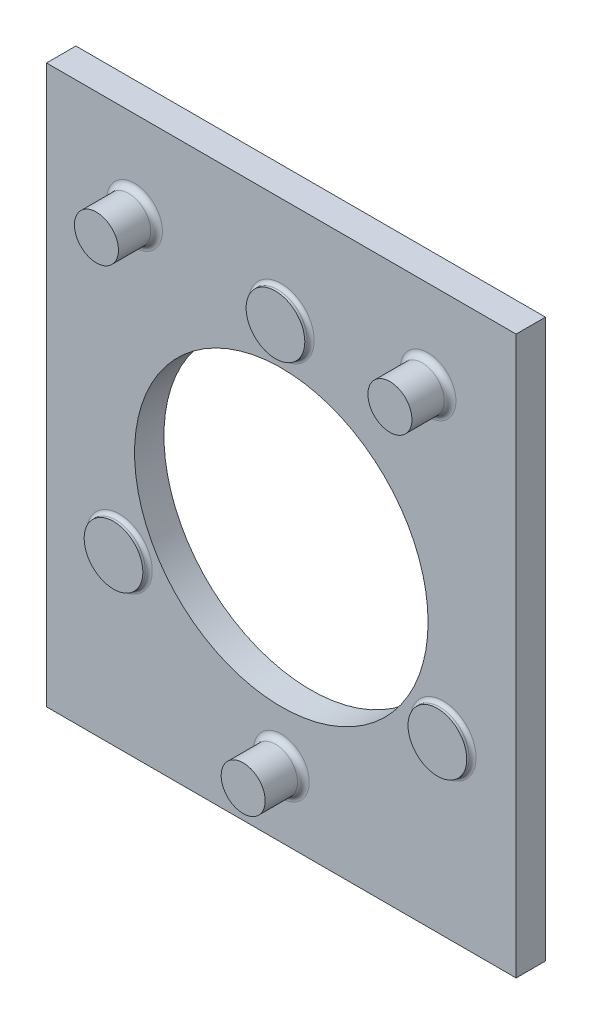
SolidWorks part; units mm, degrees
ref_plane "Front" through (0, 0, 0) normal (0, 0, 1) x (1, 0, 0)
ref_plane "Top" through (0, 0, 0) normal (0, 1, 0) x (1, 0, 0)
ref_plane "Right" through (0, 0, 0) normal (1, 0, 0) x (0, 0, -1)
sketch "Sketch1" plane through (0, 0, 0) normal (0, 0, 1) x (1, 0, 0)
  line L1 (0, 0) -> (203.2, 0)
  line L2 (0, 0) -> (0, 241.3)
  line L3 (0, 241.3) -> (203.2, 241.3)
  line L4 (203.2, 0) -> (203.2, 241.3)
  circle A0 centre (101.6, 114.3) radius 63.5
  dimension "D3" = 127
  dimension "D1" = 203.2
  dimension "D2" = 241.3
  dimension "D4" = 101.6
  dimension "D5" = 114.3
extrude "Base-Extrude" add sketch "Sketch1" along normal blind 12.7
sketch "Sketch3" plane through (0, 0, 12.7) normal (0, 0, 1) x (1, 0, 0)
  line L0 (101.6, 114.3) -> (101.6, 195.2128) construction
  line L1 (101.6, 114.3) -> (171.6725, 73.8436) construction
  line L2 (101.6, 114.3) -> (31.5275, 73.8436) construction
  circle A0 centre (31.5275, 73.8436) radius 12.7
  circle A1 centre (101.6, 195.2128) radius 12.7
  circle A2 centre (171.6725, 73.8436) radius 12.7
  circle A3 centre (101.6, 114.3) radius 63.5 construction
  circle A4 centre (101.6, 114.3) radius 63.5 construction
  circle A5 centre (101.6, 114.3) radius 80.9128 construction
  dimension "D1" = 25.4
  dimension "D2" = 25.4
  dimension "D3" = 25.4
  dimension "D4" = 161.8256
  dimension "D5" = 120
  dimension "D6" = 120
extrude "Boss-Extrude2" add sketch "Sketch3" along normal blind 2.54
sketch "Sketch4" plane through (0, 0, 12.7) normal (0, 0, 1) x (1, 0, 0)
  line L0 (203.2, 0) -> (203.2, 241.3) construction
  line L1 (203.2, 241.3) -> (0, 241.3) construction
  line L2 (0, 241.3) -> (0, 0) construction
  circle A0 centre (38.1, 203.2) radius 9.525
  circle A1 centre (165.1, 203.2) radius 9.525
  dimension "D1" = 19.05
  dimension "D4" = 19.05
  dimension "D2" = 38.1
  dimension "D3" = 38.1
  dimension "D5" = 38.1
  dimension "D6" = 38.1
extrude "Boss-Extrude4" add sketch "Sketch4" along normal blind 16.51
sketch "Sketch5" plane through (0, 0, 12.7) normal (0, 0, 1) x (1, 0, 0)
  line L0 (101.6, 0) -> (101.6, 52.9028) construction
  line L1 (0, 0) -> (203.2, 0) construction
  circle A1 centre (101.6, 28.575) radius 9.525
  dimension "D1" = 28.575
  dimension "D3" = 19.05
extrude "Boss-Extrude5" add sketch "Sketch5" along normal blind 16.51
fillet "Fillet4" radius 2.54 3 edges at (28.575, 203.2, 12.7) (155.575, 203.2, 12.7) (92.075, 28.575, 12.7)
fillet "Fillet5" radius 1.524 3 edges at (18.8275, 73.8436, 12.7) (88.9, 195.2128, 12.7) (158.9725, 73.8436, 12.7)
